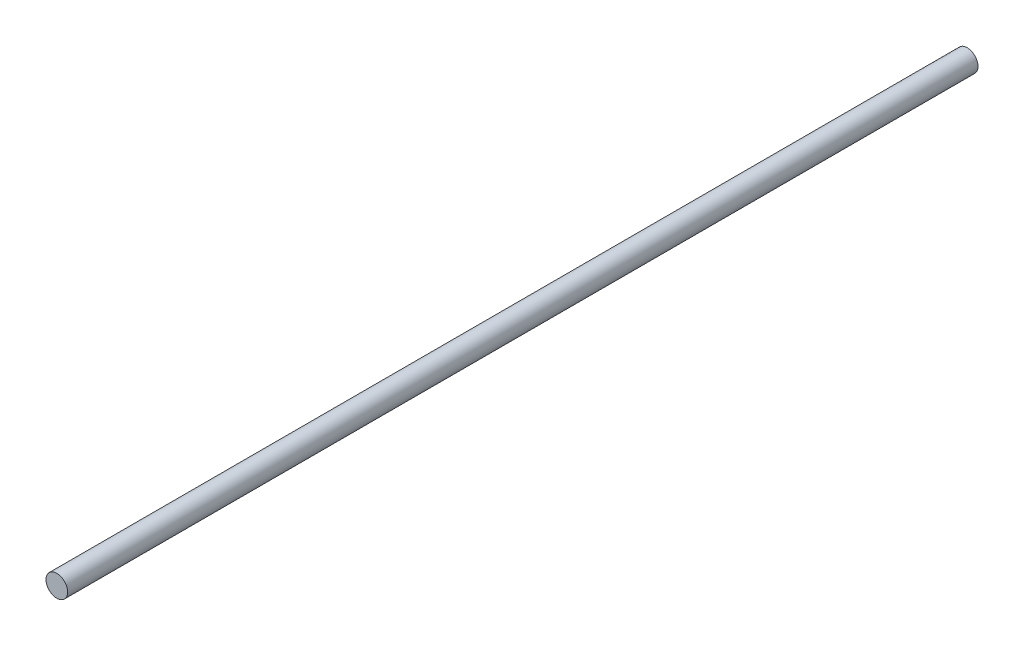
SolidWorks part; units mm, degrees
ref_plane "Front Plane" through (0, 0, 0) normal (0, 0, 1) x (1, 0, 0)
ref_plane "Top Plane" through (0, 0, 0) normal (0, 1, 0) x (1, 0, 0)
ref_plane "Right Plane" through (0, 0, 0) normal (1, 0, 0) x (0, 0, -1)
sketch "Sketch1" plane through (0, 0, 0) normal (0, 0, 1) x (1, 0, 0)
  circle A0 centre (0, 0) radius 1.9
  dimension "D1" = 3.8
extrude "Boss-Extrude1" add sketch "Sketch1" along normal blind 160
